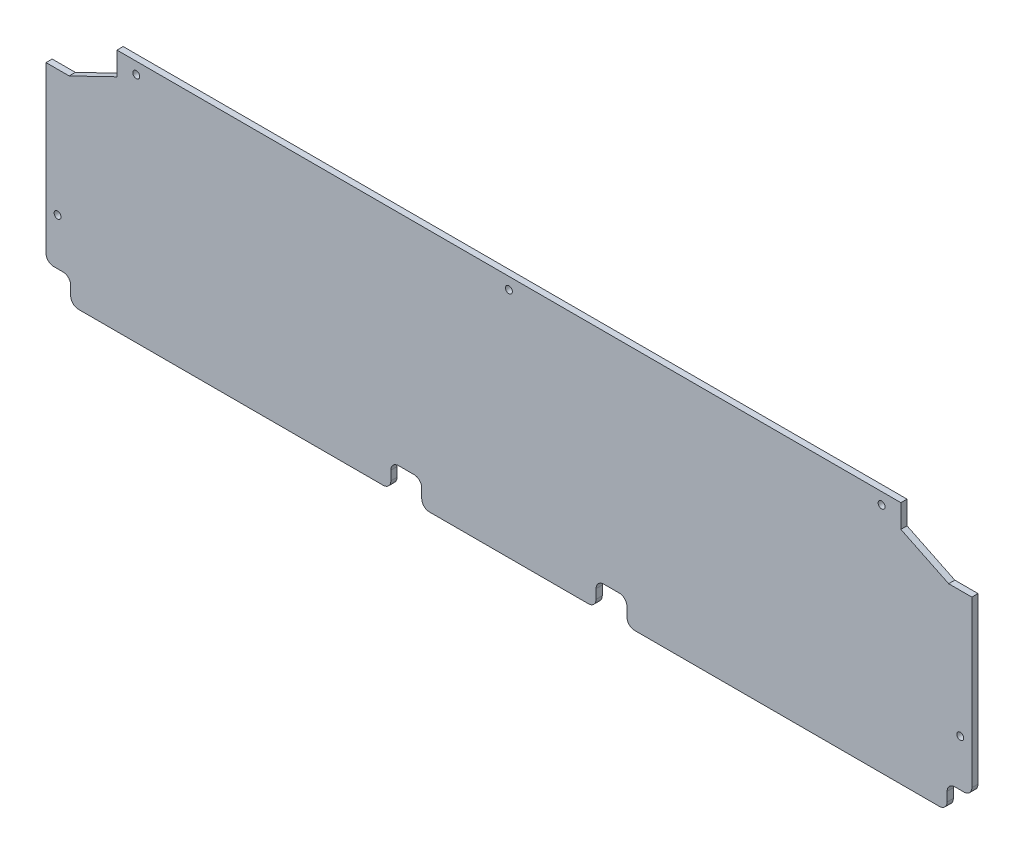
SolidWorks part; units mm, degrees
ref_plane "正面" through (0, 0, 0) normal (0, 0, 1) x (1, 0, 0)
ref_plane "平面" through (0, 0, 0) normal (0, 1, 0) x (1, 0, 0)
ref_plane "右側面" through (0, 0, 0) normal (1, 0, 0) x (0, 0, -1)
sketch "ｽｹｯﾁ1" plane through (0, 0, 0) normal (0, 0, 1) x (1, 0, 0)
  line L1 (0, 0) -> (600, 0)
  line L2 (0, 0) -> (0, 158)
  line L3 (0, 158) -> (600, 158)
  line L4 (600, 0) -> (600, 158)
  dimension "D1" = 600
  dimension "D2" = 158
extrude "ﾎﾞｽ - 押し出し1" add sketch "ｽｹｯﾁ1" along normal blind 4
sketch "ｽｹｯﾁ2" plane through (0, 0, 4) normal (0, 0, 1) x (1, 0, 0)
  line L0 (46, 158) -> (46, 143)
  line L1 (600, 158) -> (0, 158) construction
  line L2 (46, 143) -> (15, 128)
  line L3 (15, 128) -> (0, 128)
  line L4 (0, 158) -> (0, 0) construction
  line L5 (0, 128) -> (0, 158)
  line L6 (0, 158) -> (46, 158)
  line L7 (600, 158) -> (600, 128)
  line L8 (600, 0) -> (600, 158) construction
  line L9 (600, 128) -> (585, 128)
  line L10 (585, 128) -> (554, 143)
  line L11 (554, 143) -> (554, 158)
  line L12 (554, 158) -> (600, 158)
  line L13 (300, 158) -> (300, 0) construction
  line L14 (0, 0) -> (600, 0) construction
  line L15 (356.5, 0) -> (356.5, 16)
  line L16 (0, 16) -> (16, 16)
  line L17 (0, 16) -> (0, 0)
  line L18 (0, 0) -> (16, 0)
  line L19 (16, 16) -> (16, 0)
  line L20 (223.5, 0) -> (243.5, 0)
  line L21 (223.5, 0) -> (223.5, 16)
  line L22 (223.5, 16) -> (243.5, 16)
  line L23 (243.5, 0) -> (243.5, 16)
  line L24 (376.5, 16) -> (356.5, 16)
  line L25 (376.5, 0) -> (376.5, 16)
  line L26 (376.5, 0) -> (356.5, 0)
  line L27 (584, 16) -> (584, 0)
  line L28 (600, 0) -> (584, 0)
  line L29 (600, 16) -> (600, 0)
  line L30 (600, 16) -> (584, 16)
  dimension "D1" = 15
  dimension "D2" = 15
  dimension "D3" = 30
  dimension "D4" = 46
  dimension "D5" = 15
  dimension "D6" = 15
  dimension "D7" = 30
  dimension "D8" = 46
  dimension "D9" = 16
  dimension "D10" = 16
  dimension "D11" = 20
  dimension "D12" = 56.5
extrude "ｶｯﾄ - 押し出し1" cut sketch "ｽｹｯﾁ2" against normal blind 10
fillet "ﾌｨﾚｯﾄ1" radius 5 14 edges at (600, 16, 2) (584, 16, 2) (584, 0, 2) (376.5, 0, 2) (376.5, 16, 2) (356.5, 16, 2) (356.5, 0, 2) (243.5, 0, 2) (243.5, 16, 2) (223.5, 16, 2) (223.5, 0, 2) (16, 0, 2) (16, 16, 2) (0, 16, 2)
sketch "ｽｹｯﾁ3" plane through (0, 0, 4) normal (0, 0, 1) x (1, 0, 0)
  line L0 (300, 158) -> (300, 0) construction
  line L1 (554, 158) -> (46, 158) construction
  line L2 (248.5, 0) -> (351.5, 0) construction
  line L3 (600, 21) -> (600, 128) construction
  line L4 (585, 128) -> (600, 128) construction
  line L5 (554, 158) -> (554, 143) construction
  point P1 (300, 150.5)
  point P2 (541.5, 150.5)
  point P3 (592.5, 46.18)
  point P17 (7.5, 46.18)
  point P18 (58.5, 150.5)
  dimension "D1" = 7.5
  dimension "D2" = 7.5
  dimension "D3" = 81.82
  dimension "D4" = 12.5
hole_wizard "M4 すきま穴1" positions "ｽｹｯﾁ3" profile "ｽｹｯﾁ4" hole size "M4" standard "JIS" end condition through all
sketch "ｽｹｯﾁ4" plane through (58.5, 150.5, 4) normal (1, 0, 0) x (0, -1, 0)
  line L0 (0, 0) -> (0, 4)
  line L1 (0, 4) -> (2.25, 4)
  line L2 (2.25, 4) -> (2.25, 0)
  line L5 (2.25, 0) -> (0, 0)
  line L11 (0, -6.35) -> (0, 107.95) construction
  dimension "通し穴の直径" = 4.5
  dimension "通し穴の深さ" = 4
